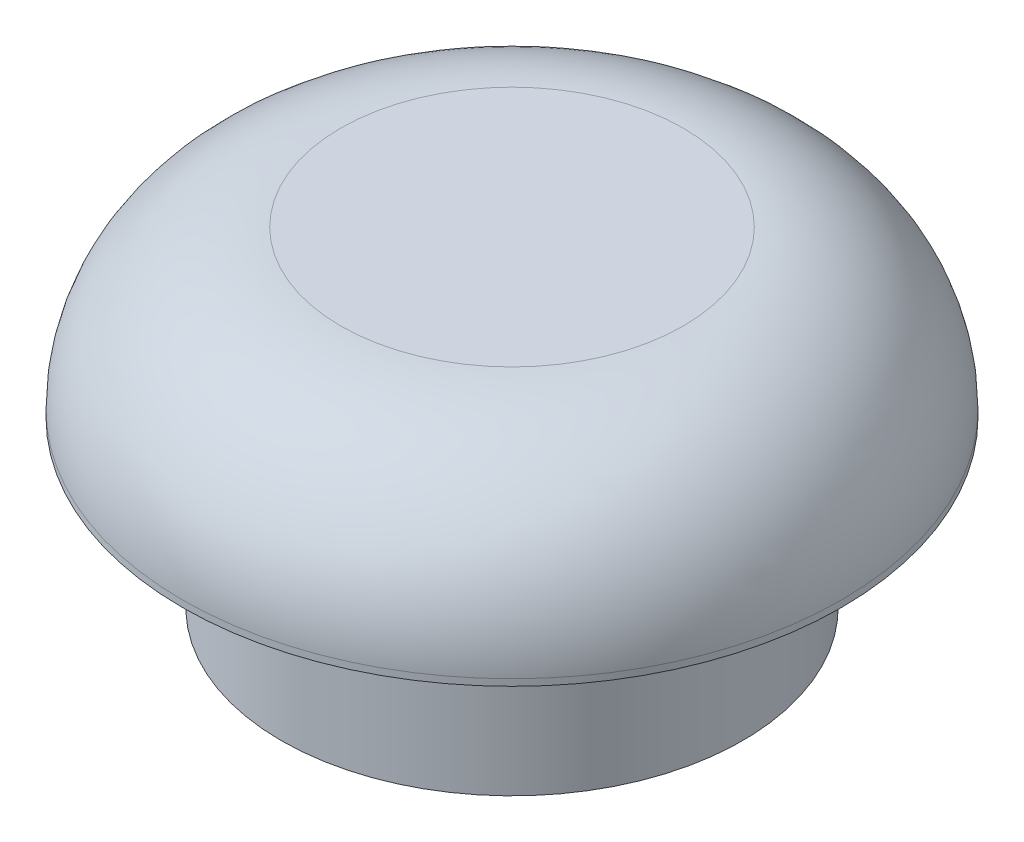
SolidWorks part; units mm, degrees
ref_plane "Plano frontal" through (0, 0, 0) normal (0, 0, 1) x (1, 0, 0)
ref_plane "Plano superior" through (0, 0, 0) normal (0, 1, 0) x (1, 0, 0)
ref_plane "Plano direito" through (0, 0, 0) normal (1, 0, 0) x (0, 0, -1)
sketch "Esboço1" plane through (0, 0, 0) normal (0, 0, 1) x (1, 0, 0)
  line L0 (0, 36.9546) -> (0, -36.9546) construction
  line L1 (-1.55, 9.2389) -> (-3.5, 9.2389)
  line L2 (-3.5, 9.2389) -> (-3.5, 11.7389)
  line L3 (-3.5, 11.7389) -> (-5, 11.7389)
  line L4 (-5, 11.7389) -> (-5, 11.8389)
  line L5 (-2.6, 14.2389) -> (0, 14.2389)
  line L6 (0, 14.2389) -> (0, 13.2389)
  line L7 (0, 13.2389) -> (-1.55, 13.2389)
  line L8 (-1.55, 13.2389) -> (-1.55, 9.2389)
  arc A0 (-2.6, 14.2389) -> (-5, 11.8389) centre (-2.6, 11.8389) ccw
  point P4 (0, 0)
  dimension "D7" = 2.4
  dimension "D1" = 2.5
  dimension "D2" = 2.5
  dimension "D3" = 3.1
  dimension "D4" = 7
  dimension "D5" = 4
  dimension "D6" = 10
revolve "Revolução1" add sketch "Esboço1" angle 360 about L0
